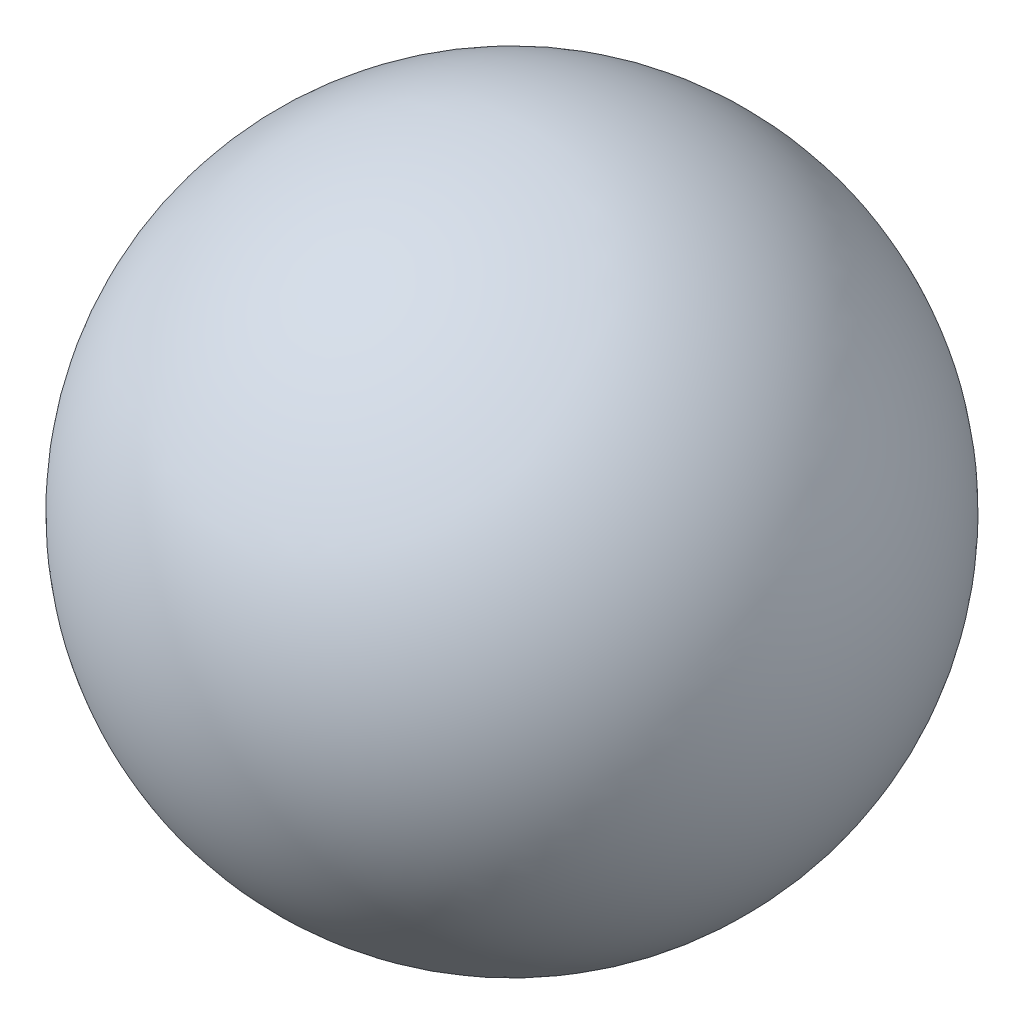
SolidWorks part; units mm, degrees
ref_plane "前视基准面" through (0, 0, 0) normal (0, 0, 1) x (1, 0, 0)
ref_plane "上视基准面" through (0, 0, 0) normal (0, 1, 0) x (1, 0, 0)
ref_plane "右视基准面" through (0, 0, 0) normal (1, 0, 0) x (0, 0, -1)
sketch "草图1" plane through (0, 0, 0) normal (0, 1, 0) x (1, 0, 0)
  line L0 (0, 0.8675) -> (0, -0.7368) construction
  circle A0 centre (0, 0) radius 0.5
  dimension "D1" = 1
revolve "旋转2" add sketch "草图1" angle 360 about L0
